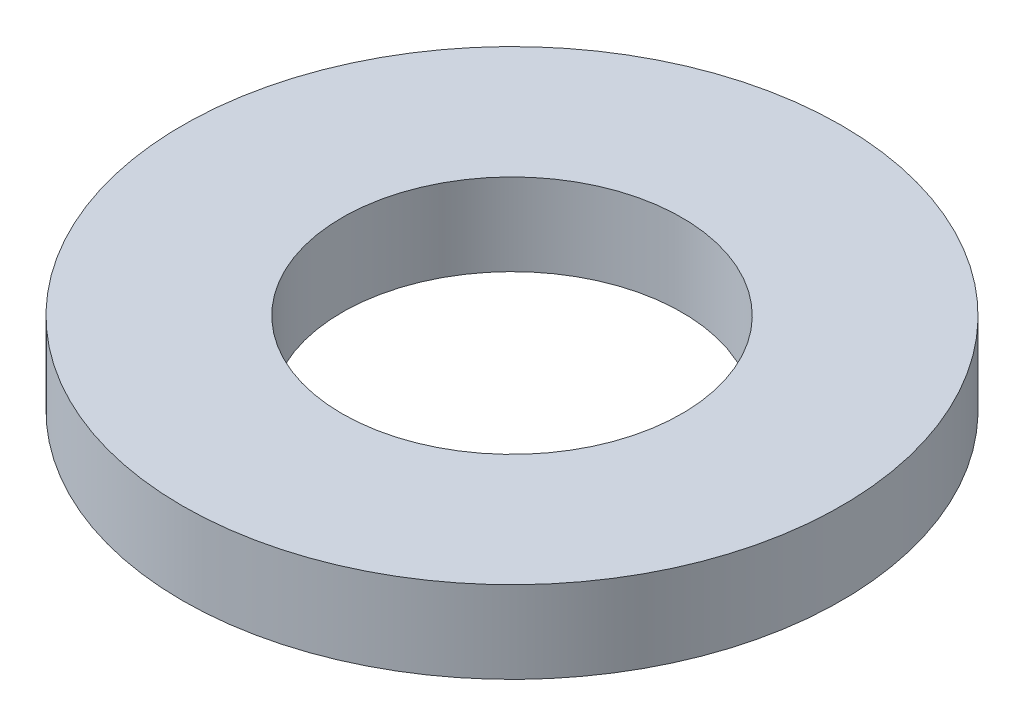
SolidWorks part; units mm, degrees
material "6061-T6 (SS)"
ref_plane "Front Plane" through (0, 0, 0) normal (0, 0, 1) x (1, 0, 0)
ref_plane "Top Plane" through (0, 0, 0) normal (0, 1, 0) x (1, 0, 0)
ref_plane "Right Plane" through (0, 0, 0) normal (1, 0, 0) x (0, 0, -1)
sketch "Sketch1" plane through (0, 0, 0) normal (0, 1, 0) x (1, 0, 0)
  circle A0 centre (0, 0) radius 2.8575
  dimension "D1" = 5.715
extrude "Boss-Extrude1" add sketch "Sketch1" along normal blind 0.7112
hole_wizard "#32 (0.116) Diameter Hole1" positions "Sketch2" profile "Sketch3" hole size "#32" standard "ANSI Inch" end condition through all
sketch "Sketch2" plane through (0, 0.7112, 0) normal (0, 1, 0) x (1, 0, 0)
  point P0 (0, 0)
sketch "Sketch3" plane through (0, 0.7112, 0) normal (1, 0, 0) x (0, 0, 1)
  line L0 (0, 0) -> (0, 0.7112)
  line L1 (0, 0.7112) -> (1.4732, 0.7112)
  line L2 (1.4732, 0.7112) -> (1.4732, 0)
  line L5 (1.4732, 0) -> (0, 0)
  line L11 (0, -6.35) -> (0, 107.95) construction
  dimension "Thru Hole Dia." = 2.9464
  dimension "Thru Hole Depth" = 0.7112
